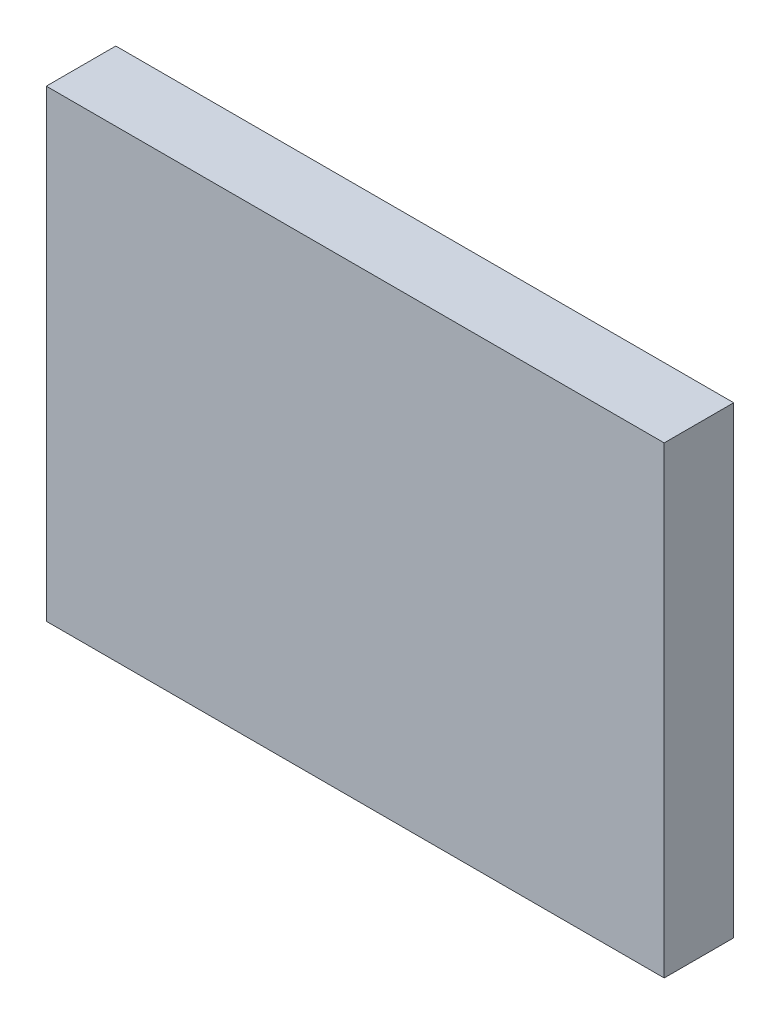
SolidWorks part; units mm, degrees
material "Balsa"
ref_plane "Front Plane" through (0, 0, 0) normal (0, 0, 1) x (1, 0, 0)
ref_plane "Top Plane" through (0, 0, 0) normal (0, 1, 0) x (1, 0, 0)
ref_plane "Right Plane" through (0, 0, 0) normal (1, 0, 0) x (0, 0, -1)
sketch "Sketch1" plane through (0, 0, 0) normal (0, 0, 1) x (1, 0, 0)
  line L1 (-80, 60) -> (80, 60)
  line L2 (-80, 60) -> (-80, -60)
  line L3 (-80, -60) -> (80, -60)
  line L4 (80, 60) -> (80, -60)
  line L5 (-80, 60) -> (80, -60) construction
  line L6 (-80, -60) -> (80, 60) construction
  point P0 (0, 0)
  dimension "D1" = 160
  dimension "D2" = 120
extrude "Boss-Extrude1" add sketch "Sketch1" along normal blind 18
